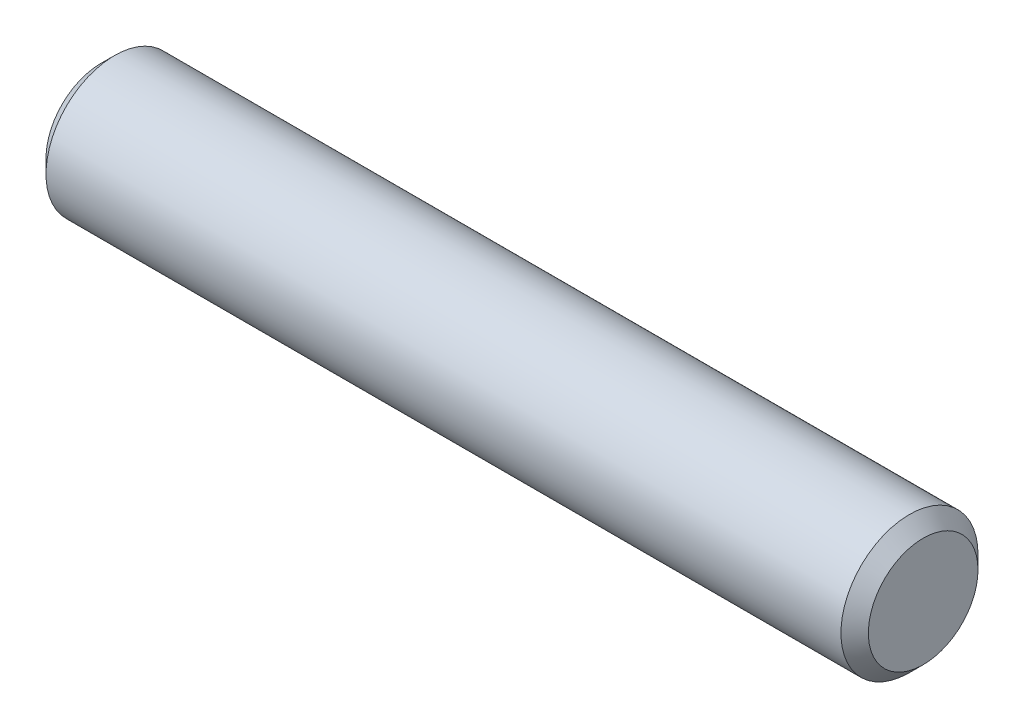
SolidWorks part; units mm, degrees
ref_plane "Front" through (0, 0, 0) normal (0, 0, 1) x (1, 0, 0)
ref_plane "Top" through (0, 0, 0) normal (0, 1, 0) x (1, 0, 0)
ref_plane "Right" through (0, 0, 0) normal (1, 0, 0) x (0, 0, -1)
sketch "Sketch1" plane through (0, 0, 0) normal (0, 0, 1) x (1, 0, 0)
  line L0 (-9.525, 0) -> (9.525, 0) construction
  line L1 (9.525, 1.5875) -> (9.525, -1.5875) construction
  line L2 (-9.525, 1.5875) -> (-9.525, -1.5875) construction
  dimension "Length" = 19.05
  dimension "Diameter" = 3.175
sketch "Sketch2" plane through (0, 0, 0) normal (1, 0, 0) x (0, 0, -1)
  circle A0 centre (0, 0) radius 1.5875
extrude "Extrude1" add sketch "Sketch2" against normal up to vertex (9.525 mm away) and the other way up to vertex (9.525 mm away) up to point (-9.525, 1.5875, 0) other way up to point (9.525, 1.5875, 0)
chamfer "Chamfer1" distance 0.3175 angle 45 2 edges at (9.525, 0, -1.5875) (-9.525, 0, -1.5875)
equation "\"D1@Chamfer1\" = \"Diameter@Sketch1\"*.1"
